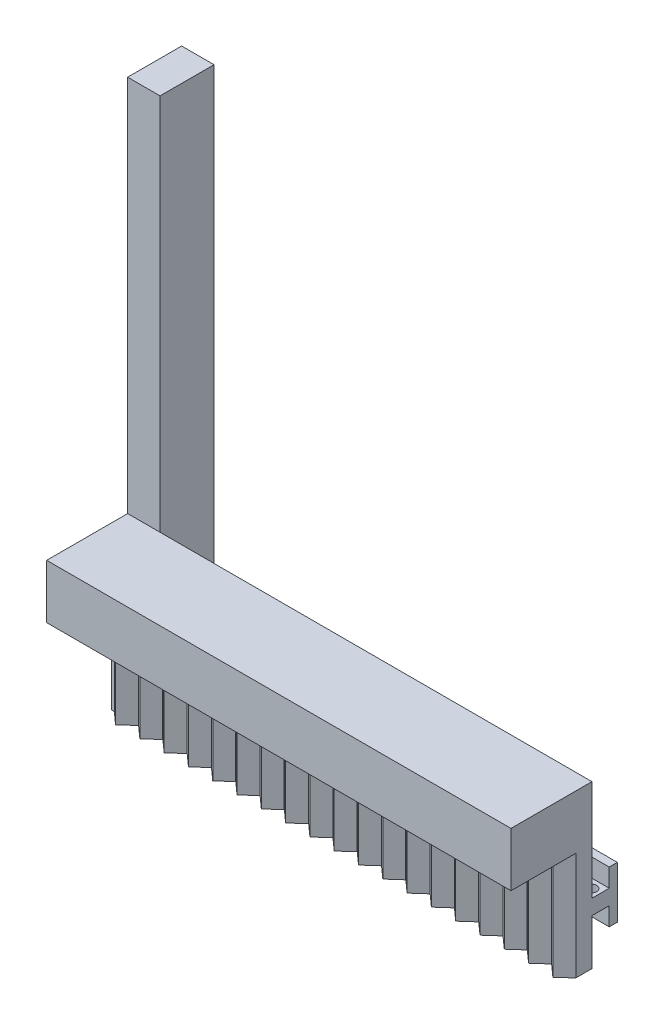
SolidWorks part; units mm, degrees
ref_plane "Front Plane" through (0, 0, 0) normal (0, 0, 1) x (1, 0, 0)
ref_plane "Top Plane" through (0, 0, 0) normal (0, 1, 0) x (1, 0, 0)
ref_plane "Right Plane" through (0, 0, 0) normal (1, 0, 0) x (0, 0, -1)
sketch "Sketch4" plane through (0, 0, 0) normal (0, 0, 1) x (1, 0, 0)
  line L1 (-6, 55.9417) -> (0, 55.9417)
  line L2 (-6, 55.9417) -> (-6, -44.0583)
  line L3 (-6, -44.0583) -> (0, -44.0583)
  line L4 (0, 55.9417) -> (0, -44.0583)
  dimension "D1" = 100
  dimension "D2" = 6
extrude "Boss-Extrude2" add sketch "Sketch4" along normal blind 10
ref_plane "Plane2" through (0, 0, 0) normal (1, 0, 0) x (0, 0, -1)
sketch "Sketch5" plane through (0, 0, 0) normal (1, 0, 0) x (0, 0, -1)
  line L0 (-10, -44.0583) -> (-10, 55.9417) construction
  line L1 (-10, -32.7583) -> (-6.8, -32.7583)
  line L2 (-10, -32.7583) -> (-10, -35.5583)
  line L3 (-10, -35.5583) -> (-6.8, -35.5583)
  line L5 (-6.8, -32.7583) -> (-6.8, -29.3583)
  line L6 (-6.8, -29.3583) -> (-5.3, -29.3583)
  line L8 (-6.8, -38.9583) -> (-5.3, -38.9583)
  line L9 (-5.3, -29.3583) -> (-5.3, -38.9583)
  line L10 (-6.8, -38.9583) -> (-6.8, -35.5583)
  line L11 (-10, -44.0583) -> (0, -44.0583) construction
  point P10 (-6.05, -29.3583)
  dimension "D1" = 3.4
  dimension "D2" = 2.8
  dimension "D3" = 1.5
  dimension "D4" = 3.2
  dimension "D5" = 3.2
  dimension "D6" = 3.4
  dimension "D7" = 5.1
extrude "Boss-Extrude3" add sketch "Sketch5" along normal blind 80
ref_plane "Plane3" through (0, 0, 10) normal (0, 0, 1) x (1, 0, 0)
sketch "Sketch6" plane through (0, 0, 10) normal (0, 0, 1) x (1, 0, 0)
  line L1 (-6, -44.0583) -> (80, -44.0583)
  line L2 (-6, -44.0583) -> (-6, -24.0583)
  line L3 (-6, -24.0583) -> (80, -24.0583)
  line L4 (80, -44.0583) -> (80, -24.0583)
  dimension "D1" = 86
  dimension "D2" = 20
extrude "Boss-Extrude4" add sketch "Sketch6" along normal blind 3
ref_plane "Plane4" through (0, -35.5583, 0) normal (0, -1, 0) x (-1, 0, 0)
sketch "Sketch7" plane through (0, -35.5583, 0) normal (0, -1, 0) x (-1, 0, 0)
  circle A0 centre (-78.3622, -8.5334) radius 1.0267
extrude "Cut-Extrude2" cut sketch "Sketch7" against normal blind 10
ref_plane "Plane5" through (0, -24.0583, 0) normal (0, 1, 0) x (1, 0, 0)
sketch "Sketch8" plane through (0, -24.0583, 0) normal (0, 1, 0) x (1, 0, 0)
  line L7 (80, -13) -> (-6, -13) construction
  line L8 (80, -13) -> (77.7639, -15)
  line L9 (77.7639, -15) -> (75.5279, -13)
  line L10 (75.5279, -13) -> (80, -13)
  line L12 (75.5, -13) -> (73.2639, -15)
  line L13 (73.2639, -15) -> (71.0279, -13)
  line L14 (71.0279, -13) -> (75.5, -13)
  line L16 (71, -13) -> (68.7639, -15)
  line L17 (68.7639, -15) -> (66.5279, -13)
  line L18 (66.5279, -13) -> (71, -13)
  line L20 (66.5, -13) -> (64.2639, -15)
  line L21 (64.2639, -15) -> (62.0279, -13)
  line L22 (62.0279, -13) -> (66.5, -13)
  line L24 (62, -13) -> (59.7639, -15)
  line L25 (59.7639, -15) -> (57.5279, -13)
  line L26 (57.5279, -13) -> (62, -13)
  line L28 (57.5, -13) -> (55.2639, -15)
  line L29 (55.2639, -15) -> (53.0279, -13)
  line L30 (53.0279, -13) -> (57.5, -13)
  line L32 (53, -13) -> (50.7639, -15)
  line L33 (50.7639, -15) -> (48.5279, -13)
  line L34 (48.5279, -13) -> (53, -13)
  line L36 (48.5, -13) -> (46.2639, -15)
  line L37 (46.2639, -15) -> (44.0279, -13)
  line L38 (44.0279, -13) -> (48.5, -13)
  line L40 (44, -13) -> (41.7639, -15)
  line L41 (41.7639, -15) -> (39.5279, -13)
  line L42 (39.5279, -13) -> (44, -13)
  line L44 (39.5, -13) -> (37.2639, -15)
  line L45 (37.2639, -15) -> (35.0279, -13)
  line L46 (35.0279, -13) -> (39.5, -13)
  line L48 (35, -13) -> (32.7639, -15)
  line L49 (32.7639, -15) -> (30.5279, -13)
  line L50 (30.5279, -13) -> (35, -13)
  line L52 (30.5, -13) -> (28.2639, -15)
  line L53 (28.2639, -15) -> (26.0279, -13)
  line L54 (26.0279, -13) -> (30.5, -13)
  line L56 (26, -13) -> (23.7639, -15)
  line L57 (23.7639, -15) -> (21.5279, -13)
  line L58 (21.5279, -13) -> (26, -13)
  line L60 (21.5, -13) -> (19.2639, -15)
  line L61 (19.2639, -15) -> (17.0279, -13)
  line L62 (17.0279, -13) -> (21.5, -13)
  line L64 (17, -13) -> (14.7639, -15)
  line L65 (14.7639, -15) -> (12.5279, -13)
  line L66 (12.5279, -13) -> (17, -13)
  line L68 (12.5, -13) -> (10.2639, -15)
  line L69 (10.2639, -15) -> (8.0279, -13)
  line L70 (8.0279, -13) -> (12.5, -13)
  line L72 (8, -13) -> (5.7639, -15)
  line L73 (5.7639, -15) -> (3.5279, -13)
  line L74 (3.5279, -13) -> (8, -13)
  line L76 (3.5, -13) -> (1.2639, -15)
  line L77 (1.2639, -15) -> (-0.9721, -13)
  line L78 (-0.9721, -13) -> (3.5, -13)
  line L80 (-1, -13) -> (-3.2361, -15)
  line L81 (-3.2361, -15) -> (-5.4721, -13)
  line L82 (-5.4721, -13) -> (-1, -13)
  point P10 (33.9408, -14)
  dimension "D2" = 3
  dimension "D3" = 3
  dimension "D4" = 19
extrude "Boss-Extrude6" add sketch "Sketch8" against normal blind 20
sketch "Sketch9" plane through (0, 0, 0) normal (1, 0, 0) x (0, 0, -1)
  line L0 (-10, -24.0583) -> (3.1594, -24.0583)
  line L1 (3.1594, -24.0583) -> (3.1594, -44.0583)
  line L2 (-10, -44.0583) -> (0, -44.0583) construction
  line L3 (3.1594, -44.0583) -> (-10, -44.0583)
  line L4 (-10, -44.0583) -> (-10, -35.5583)
  line L5 (-10, -35.5583) -> (-6.8, -35.5583)
  line L6 (-6.8, -35.5583) -> (-6.8, -39.0675)
  line L7 (-6.8, -39.0675) -> (-5.2004, -39.0675)
  line L8 (-5.2004, -39.0675) -> (-5.2004, -29.4559)
  line L9 (-5.2004, -29.4559) -> (-6.8, -29.4559)
  line L10 (-6.8, -29.4559) -> (-6.8, -32.7583)
  line L11 (-6.8, -32.7583) -> (-10, -32.7583)
  line L12 (-10, -32.7583) -> (-10, -24.0583)
extrude "Cut-Extrude3" cut sketch "Sketch9" against normal blind 10
ref_plane "Plane6" through (0, 0, 10) normal (0, 0, 1) x (1, 0, 0)
sketch "Sketch11" plane through (0, 0, 10) normal (0, 0, 1) x (1, 0, 0)
  line L0 (-6, 55.9417) -> (-6, -24.0583) construction
  line L1 (80, -24.0583) -> (-6, -24.0583)
  line L2 (80, -24.0583) -> (80, -14.0583)
  line L3 (80, -14.0583) -> (-6, -14.0583)
  line L4 (-6, -24.0583) -> (-6, -14.0583)
  dimension "D1" = 10
extrude "Boss-Extrude7" add sketch "Sketch11" along normal blind 15
